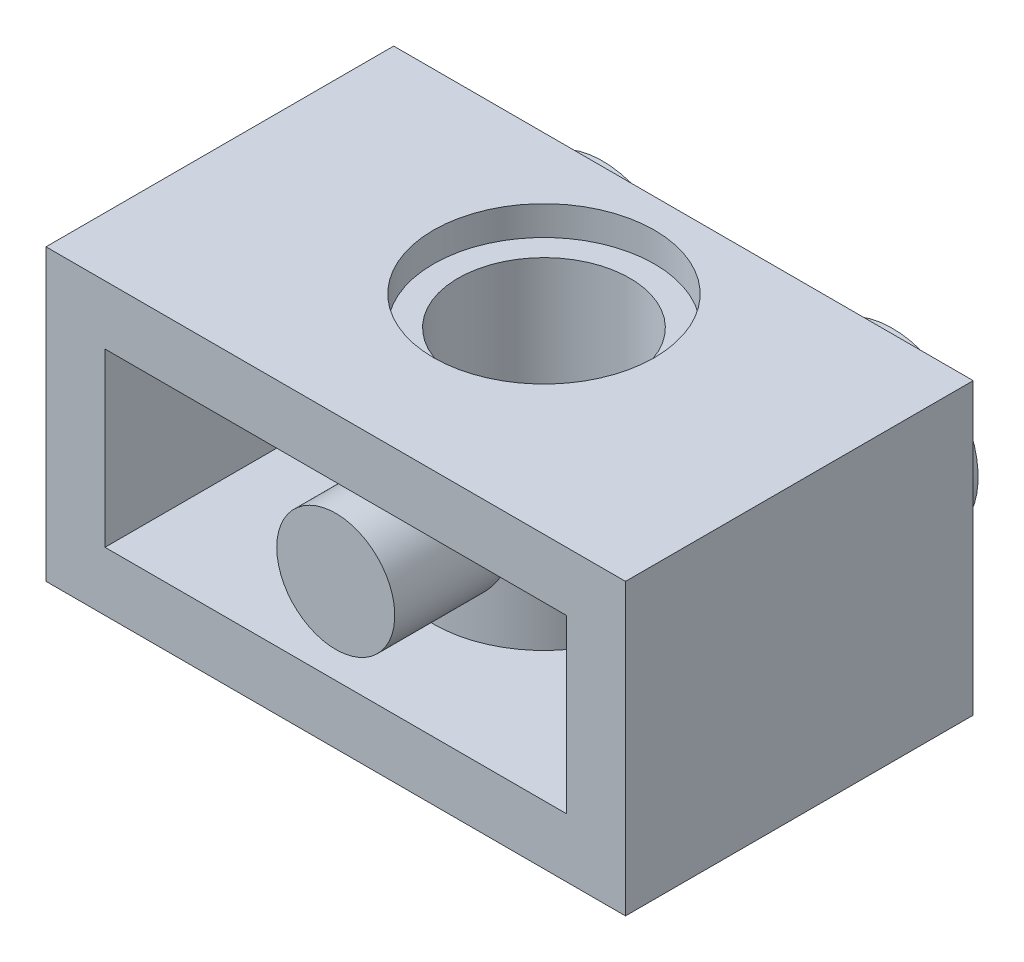
SolidWorks part; units mm, degrees
material "Custom Plastic"
ref_plane "Front Plane" through (0, 0, 0) normal (0, 0, 1) x (1, 0, 0)
ref_plane "Top Plane" through (0, 0, 0) normal (0, 1, 0) x (1, 0, 0)
ref_plane "Right Plane" through (0, 0, 0) normal (1, 0, 0) x (0, 0, -1)
ref_plane "Plane1" through (0, 4.0325, 0) normal (0, 1, 0) x (-1, 0, 0)
sketch "Sketch1" plane through (0, 4.0325, 0) normal (0, 1, 0) x (-1, 0, 0)
  line L0 (-8.065, 4.839) -> (-8.065, -4.839)
  line L1 (-8.065, -4.839) -> (8.065, -4.839)
  line L2 (8.065, -4.839) -> (8.065, 4.839)
  line L3 (8.065, 4.839) -> (-8.065, 4.839)
extrude "Boss-Extrude1" add sketch "Sketch1" against normal blind 8.065
sketch "Sketch2" plane through (0, 0, 4.839) normal (0, 0, 1) x (1, 0, 0)
  line L0 (-6.4225, -2.39) -> (6.4225, -2.39)
  line L1 (6.4225, -2.39) -> (6.4225, 2.39)
  line L2 (6.4225, 2.39) -> (-6.4225, 2.39)
  line L3 (-6.4225, 2.39) -> (-6.4225, -2.39)
extrude "Cut-Extrude1" cut sketch "Sketch2" against normal blind 8.0355
sketch "Sketch3" plane through (0, 2.39, 0) normal (0, -1, 0) x (1, 0, 0)
  line L0 (2.1061, -3.1965) -> (-2.1061, -3.1965)
  arc A0 (-2.1061, -3.1965) -> (2.1061, -3.1965) centre (0, -0.956) cw
extrude "Boss-Extrude2" add sketch "Sketch3" along normal blind 4.78
ref_plane "Plane2" through (0, 0, 0) normal (0, -1, 0) x (1, 0, 0)
sketch "Sketch4" plane through (0, 0, 0) normal (0, -1, 0) x (1, 0, 0)
  line L0 (6.4225, -4.839) -> (4.0325, -4.839)
  line L1 (4.0325, -4.839) -> (4.0325, -6.619)
  line L2 (4.0325, -6.619) -> (6.4225, -6.619)
  line L3 (6.4225, -6.619) -> (6.4225, -4.839)
  line L4 (4.0325, -4.839) -> (4.0325, -6.619) construction
revolve "Revolve1" add sketch "Sketch4" angle 360 about L4
sketch "Sketch5" plane through (0, 0, 0) normal (0, -1, 0) x (1, 0, 0)
  line L0 (-1.6425, -4.839) -> (-4.0325, -4.839)
  line L1 (-4.0325, -4.839) -> (-4.0325, -6.619)
  line L2 (-4.0325, -6.619) -> (-1.6425, -6.619)
  line L3 (-1.6425, -6.619) -> (-1.6425, -4.839)
  line L4 (-4.0325, -4.839) -> (-4.0325, -6.619) construction
revolve "Revolve2" add sketch "Sketch5" angle 360 about L4
ref_plane "Plane3" through (0, 0, -0.956) normal (0, 0, -1) x (-1, 0, 0)
sketch "Sketch6" plane through (0, 0, -0.956) normal (0, 0, -1) x (-1, 0, 0)
  line L0 (-3.075, -4.0325) -> (0, -4.0325)
  line L1 (0, -4.0325) -> (0, 4.0325)
  line L2 (0, 4.0325) -> (-3.075, 4.0325)
  line L3 (-3.075, 4.0325) -> (-3.075, 3.2175)
  line L4 (-3.075, 3.2175) -> (-2.39, 3.2175)
  line L5 (-2.39, 3.2175) -> (-2.39, -3.2175)
  line L6 (-2.39, -3.2175) -> (-3.075, -3.2175)
  line L7 (-3.075, -3.2175) -> (-3.075, -4.0325)
  line L8 (0, -4.0325) -> (0, 4.0325) construction
revolve "Cut-Revolve1" cut sketch "Sketch6" angle 360 about L8
sketch "Sketch7" plane through (0, 0, 0) normal (0, 1, 0) x (1, 0, 0)
  line L0 (-1.6425, -4.839) -> (0, -4.839)
  line L1 (0, -4.839) -> (0, -1.6436)
  line L2 (0, -1.6436) -> (-1.6425, -1.6436)
  line L3 (-1.6425, -1.6436) -> (-1.6425, -4.839)
  line L4 (0, -4.839) -> (0, -1.6436) construction
revolve "Revolve3" add sketch "Sketch7" angle 360 about L4
hole_wizard "M3 Clearance Hole1" positions "Sketch9" profile "Sketch8" hole size "M3" standard "Ansi Metric"
sketch "Sketch9" plane through (0, 0, -6.619) normal (0, 0, -1) x (-1, 0, 0)
  point P0 (4.0325, 0)
  point P1 (-4.0325, 0)
sketch "Sketch8" plane through (-4.0325, 0, -6.619) normal (1, 0, 0) x (0, 1, 0)
  line L0 (0, 0) -> (0, 1.78)
  line L1 (0, 1.78) -> (1.6425, 1.78)
  line L2 (1.6425, 1.78) -> (1.6425, 0)
  line L5 (1.6425, 0) -> (0, 0)
  line L10 (0, 1.78) -> (-1.6425, 1.78) construction
  line L11 (0, -6.35) -> (0, 107.95) construction
  dimension "Hole Dia." = 3.285
  dimension "Hole Depth" = 1.78
  dimension "Drill Angle" = 180
